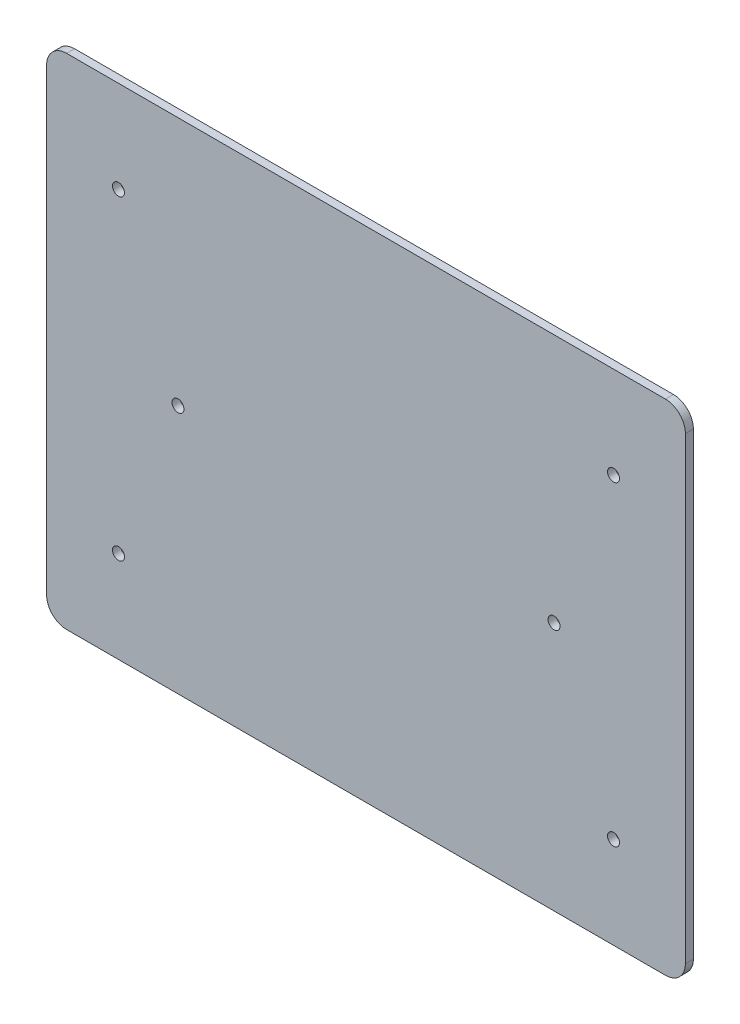
SolidWorks part; units mm, degrees
material "Cobre"
ref_plane "Plano frontal" through (0, 0, 0) normal (0, 0, 1) x (1, 0, 0)
ref_plane "Plano superior" through (0, 0, 0) normal (0, 1, 0) x (1, 0, 0)
ref_plane "Plano direito" through (0, 0, 0) normal (1, 0, 0) x (0, 0, -1)
sketch "Esboço1" plane through (0, 0, 0) normal (0, 0, 1) x (1, 0, 0)
  line L1 (47.3676, -148.0271) -> (-102.6324, -148.0271)
  line L2 (52.3676, -143.0271) -> (52.3676, -28.0271)
  line L3 (47.3676, -23.0271) -> (-102.6324, -23.0271)
  line L4 (-107.6324, -143.0271) -> (-107.6324, -28.0271)
  arc A0 (-102.6324, -148.0271) -> (-107.6324, -143.0271) centre (-102.6324, -143.0271) cw
  arc A1 (-102.6324, -23.0271) -> (-107.6324, -28.0271) centre (-102.6324, -28.0271) ccw
  arc A2 (52.3676, -28.0271) -> (47.3676, -23.0271) centre (47.3676, -28.0271) ccw
  arc A3 (47.3676, -148.0271) -> (52.3676, -143.0271) centre (47.3676, -143.0271) ccw
  point P6 (-107.6324, -148.0271)
  point P9 (-107.6324, -23.0271)
  point P14 (52.3676, -148.0271)
  dimension "D3" = 5
  dimension "D1" = 160
  dimension "D2" = 125
extrude "Ressalto-extrusão1" add sketch "Esboço1" along normal blind 2
sketch "Esboço2" plane through (0, 0, 0) normal (0, 0, -1) x (-1, 0, 0)
  line L0 (27.6324, -148.0271) -> (27.6324, -116.7121) construction
  line L2 (102.6324, -148.0271) -> (-47.3676, -148.0271) construction
  line L4 (-52.3676, -143.0271) -> (-52.3676, -28.0271) construction
  circle A0 centre (-34.3676, -125.0271) radius 1.5
  circle A1 centre (-19.4676, -85.5271) radius 1.5
  circle A2 centre (-34.3676, -46.0271) radius 1.5
  circle A3 centre (89.6324, -46.0271) radius 1.5
  circle A4 centre (74.7324, -85.5271) radius 1.5
  circle A5 centre (89.6324, -125.0271) radius 1.5
  dimension "D1" = 79
  dimension "D2" = 14.9
  dimension "D3" = 39.5
  dimension "D4" = 3
  dimension "D5" = 3
  dimension "D6" = 3
  dimension "D7" = 23
  dimension "D8" = 18
  dimension "D9" = 18
extrude "Corte-extrusão1" cut sketch "Esboço2" against normal blind 10
